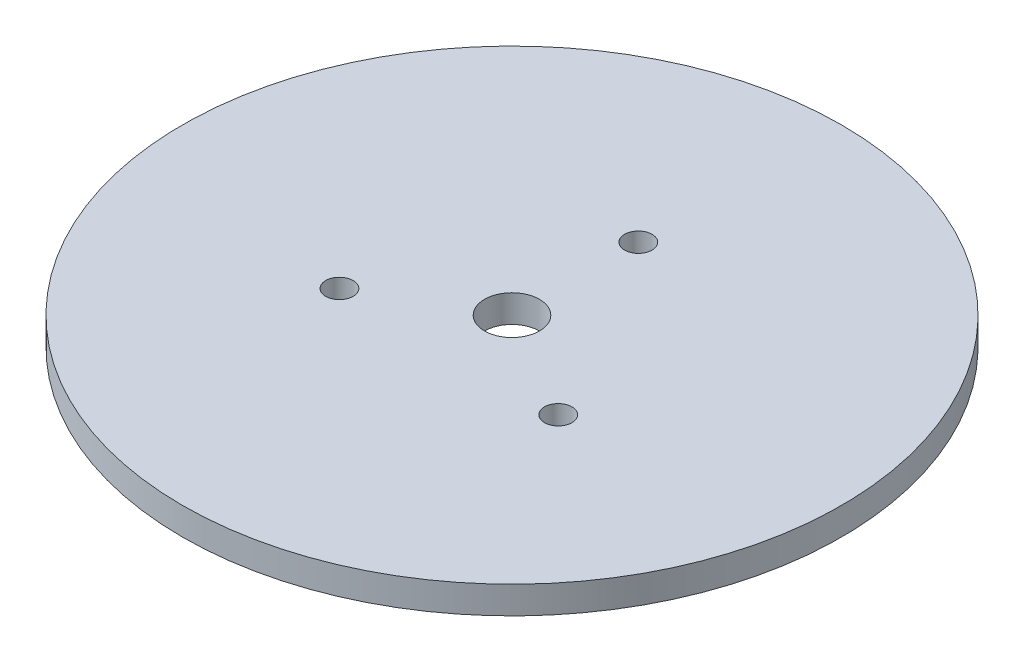
SolidWorks part; units mm, degrees
ref_plane "Front Plane" through (0, 0, 0) normal (0, 0, 1) x (1, 0, 0)
ref_plane "Top Plane" through (0, 0, 0) normal (0, 1, 0) x (1, 0, 0)
ref_plane "Right Plane" through (0, 0, 0) normal (1, 0, 0) x (0, 0, -1)
sketch "Sketch1" plane through (0, 0, 0) normal (0, 1, 0) x (1, 0, 0)
  circle A0 centre (0, 0) radius 60
  circle A1 centre (0, 0) radius 5
  circle A2 centre (0, 23) radius 2.5
  circle A3 centre (19.9186, -11.5) radius 2.5
  circle A4 centre (-19.9186, -11.5) radius 2.5
extrude "Boss-Extrude1" add sketch "Sketch1" along normal blind 5
